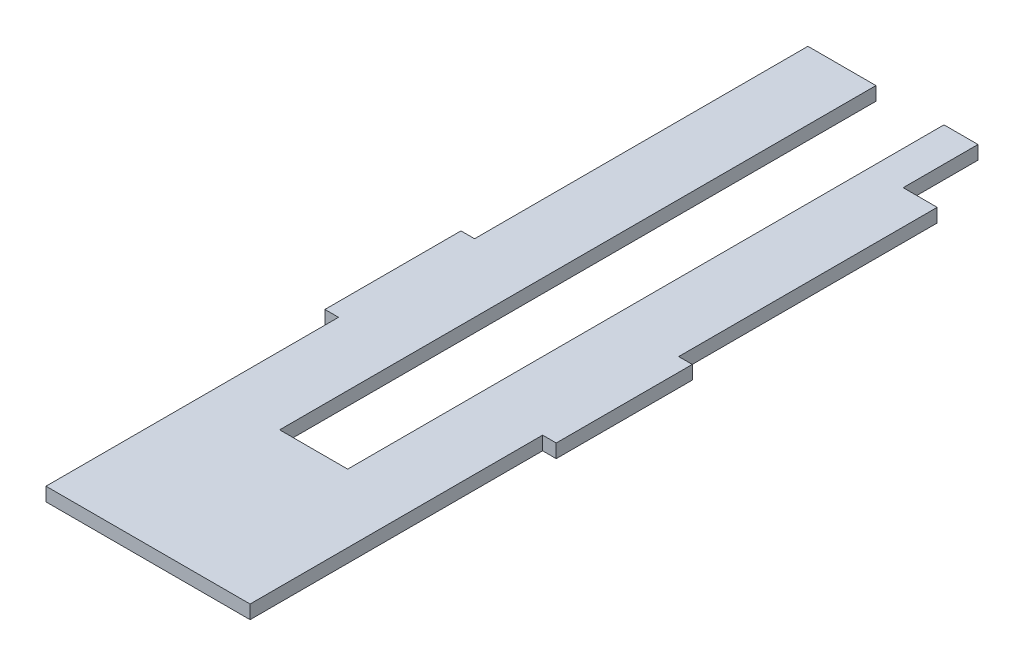
SolidWorks part; units mm, degrees
ref_plane "Front Plane" through (0, 0, 0) normal (0, 0, 1) x (1, 0, 0)
ref_plane "Top Plane" through (0, 0, 0) normal (0, 1, 0) x (1, 0, 0)
ref_plane "Right Plane" through (0, 0, 0) normal (1, 0, 0) x (0, 0, -1)
sketch "Sketch1" plane through (0, 0, 0) normal (0, 1, 0) x (1, 0, 0)
  line L0 (-75, 215) -> (-75, 0)
  line L1 (75, 215) -> (75, 0)
  line L2 (-75, 560) -> (-25, 560)
  line L3 (-75, 215) -> (-85, 215)
  line L4 (-85, 215) -> (-85, 315)
  line L5 (-85, 315) -> (-75, 315)
  line L6 (-75, 315) -> (-75, 560)
  line L7 (25, 560) -> (75, 560)
  line L8 (75, 215) -> (85, 215)
  line L9 (85, 215) -> (85, 315)
  line L10 (85, 315) -> (75, 315)
  line L11 (75, 315) -> (75, 560)
  line L13 (-25, 560) -> (-25, 121.727)
  line L14 (-25, 121.727) -> (25, 121.727)
  line L15 (-75, 0) -> (75, 0)
  line L16 (25, 560) -> (25, 121.727)
extrude "Boss-Extrude1" add sketch "Sketch1" along normal blind 10
sketch "Sketch2" plane through (0, 10, 0) normal (0, 1, 0) x (1, 0, 0)
  line L1 (75, 560) -> (50, 560)
  line L2 (75, 560) -> (75, 505)
  line L3 (75, 505) -> (50, 505)
  line L4 (50, 560) -> (50, 505)
extrude "Cut-Extrude1" cut sketch "Sketch2" against normal blind 10
